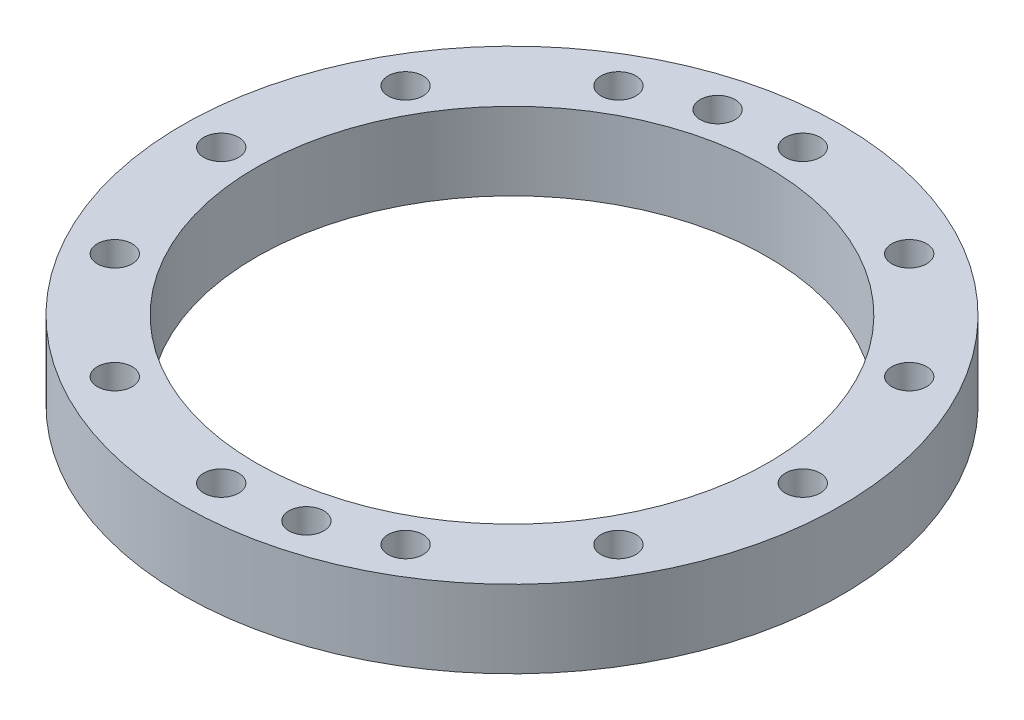
SolidWorks part; units mm, degrees
ref_plane "Front Plane" through (0, 0, 0) normal (0, 0, 1) x (1, 0, 0)
ref_plane "Top Plane" through (0, 0, 0) normal (0, 1, 0) x (1, 0, 0)
ref_plane "Right Plane" through (0, 0, 0) normal (1, 0, 0) x (0, 0, -1)
sketch "Sketch1" plane through (0, 0, 0) normal (0, 1, 0) x (1, 0, 0)
  circle A0 centre (0, 0) radius 42.5
  circle A1 centre (0, 0) radius 33
  dimension "D1" = 85
  dimension "D2" = 66
extrude "Boss-Extrude1" add sketch "Sketch1" along normal blind 10
sketch "Sketch2" plane through (0, 10, 0) normal (0, 1, 0) x (1, 0, 0)
  circle A0 centre (0, 37.5) radius 2.25
  dimension "D1" = 4.5
  dimension "D2" = 37.5
extrude "Cut-Extrude1" cut sketch "Sketch2" against normal through all
pattern_circular "CirPattern1" count 12 over 360 about axis through (0, 0, 0) along (0, 1, 0) of "Cut-Extrude1"
sketch "Sketch3" plane through (0, 10, 0) normal (0, 1, 0) x (1, 0, 0)
  line L0 (0, 0) -> (0, 37.5) construction
  line L1 (0, 0) -> (-9.7057, 36.2222) construction
  circle A0 centre (0, 0) radius 37.5 construction
  circle A1 centre (-9.7057, 36.2222) radius 2.25
  dimension "D2" = 4.5
  dimension "D1" = 15
extrude "Cut-Extrude2" cut sketch "Sketch3" against normal through all
pattern_circular "CirPattern2" count 2 over 360 about axis through (0, 0, 0) along (0, 1, 0) of "Cut-Extrude2"
